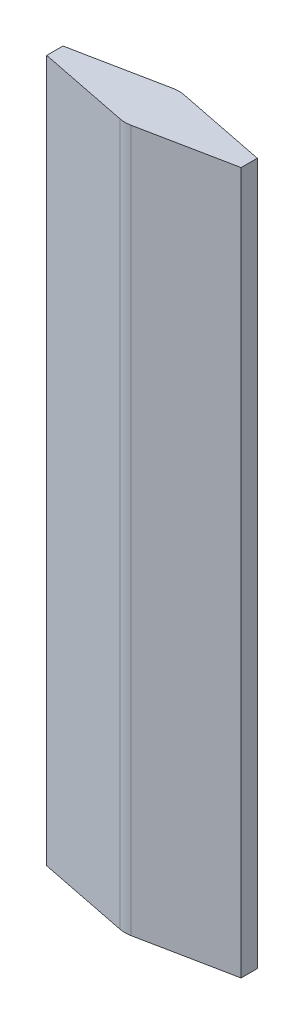
SolidWorks part; units mm, degrees
other "相机2"
other "相机3"
material "PEN"
ref_plane "前视基准面" through (0, 0, 0) normal (0, 0, 1) x (1, 0, 0)
ref_plane "上视基准面" through (0, 0, 0) normal (0, 1, 0) x (1, 0, 0)
ref_plane "右视基准面" through (0, 0, 0) normal (1, 0, 0) x (0, 0, -1)
sketch "草图4" plane through (0, 0, 0) normal (0, 1, 0) x (1, 0, 0)
  line L5 (-250, 0) -> (-9.604, -48.0496)
  line L7 (9.604, -48.0496) -> (250, 0)
  line L8 (250, 0) -> (9.604, 48.0496)
  line L9 (-9.604, 48.0496) -> (-250, 0)
  arc A2 (-9.604, -48.0496) -> (9.604, -48.0496) centre (0, 0) ccw
  arc A3 (9.604, 48.0496) -> (-9.604, 48.0496) centre (0, 0) ccw
sketch "草图5" plane through (0, 0, 0) normal (0, 1, 0) x (1, 0, 0)
  line L0 (180, 0) -> (180, -15.0112)
  line L5 (-180, 0) -> (-180, 15.0112)
  line L7 (180, 0) -> (180, 15.0112)
  line L8 (-255.102, 0) -> (-9.8, -49.0302)
  line L9 (9.8, -49.0302) -> (255.102, 0)
  line L10 (255.102, 0) -> (9.8, 49.0302)
  line L11 (-9.8, 49.0302) -> (-255.102, 0)
  line L12 (-180, -15.0112) -> (-9.8, -49.0302)
  line L13 (9.8, -49.0302) -> (180, -15.0112)
  line L14 (180, 15.0112) -> (9.8, 49.0302)
  line L15 (-9.8, 49.0302) -> (-180, 15.0112)
  line L16 (-180, 0) -> (-180, -15.0112)
  arc A4 (-9.8, -49.0302) -> (9.8, -49.0302) centre (0, 0) ccw
  arc A5 (9.8, 49.0302) -> (-9.8, 49.0302) centre (0, 0) ccw
  arc A6 (-9.8, -49.0302) -> (9.8, -49.0302) centre (0, 0) ccw
  arc A7 (9.8, 49.0302) -> (-9.8, 49.0302) centre (0, 0) ccw
  dimension "D1" = 1
extrude "凸台-拉伸1" add sketch "草图5" along normal mid plane 1300
